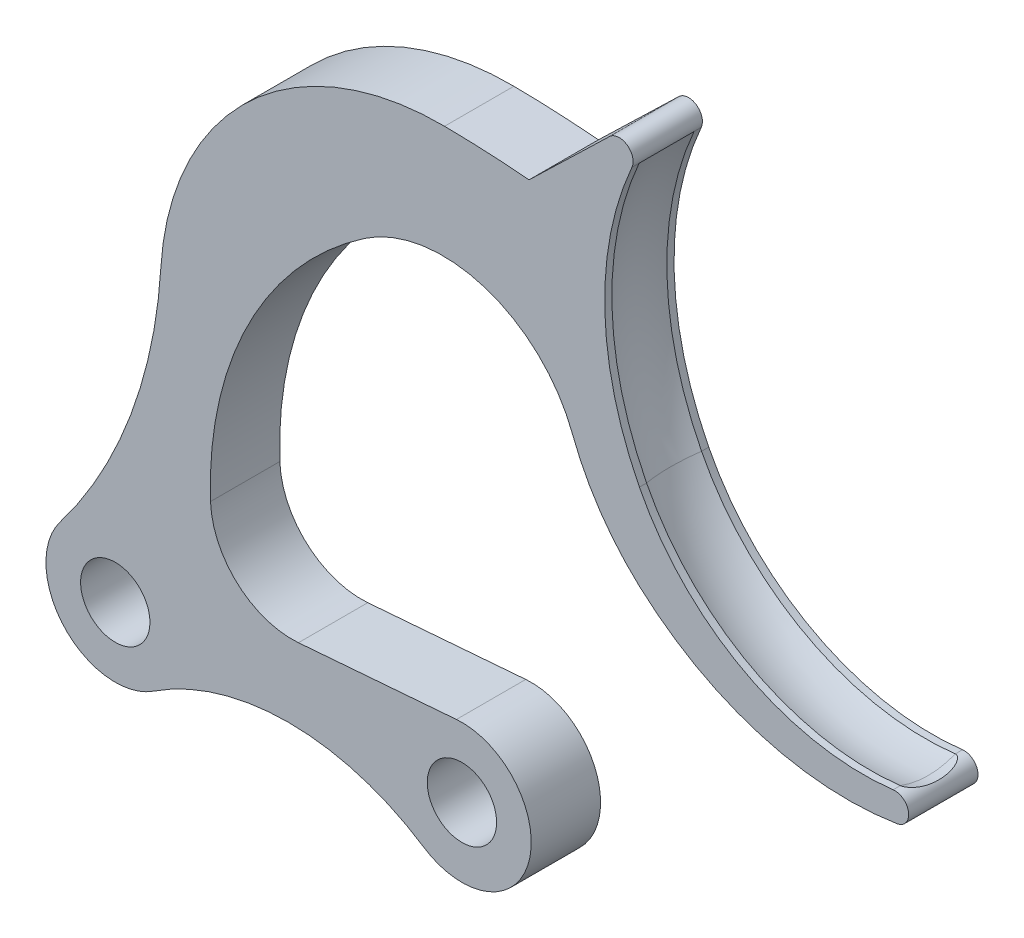
SolidWorks part; units mm, degrees
ref_plane "前基準面" through (0, 0, 0) normal (0, 0, 1) x (1, 0, 0)
ref_plane "上基準面" through (0, 0, 0) normal (0, 1, 0) x (1, 0, 0)
ref_plane "右基準面" through (0, 0, 0) normal (1, 0, 0) x (0, 0, -1)
sketch "草圖1" plane through (0, 0, 0) normal (0, 0, 1) x (1, 0, 0)
  line L0 (0, 0) -> (4.7, 36.1961) construction
  line L1 (4.7, 36.1961) -> (25, 0) construction
  line L2 (25, 0) -> (0, 0) construction
  line L3 (0, -5) -> (25, -5)
  line L4 (29.361, 2.4458) -> (15.0641, 27.938)
  line L5 (-1.4143, 27.938) -> (-4.9584, 0.6438)
  line L6 (15.0641, 27.938) -> (44.9947, 27.938)
  line L7 (-20.7636, 63.3928) -> (44.9947, 63.3928)
  line L8 (-20.7636, 63.3928) -> (-20.7636, 27.938)
  line L9 (-20.7636, 27.938) -> (-1.4143, 27.938)
  line L10 (44.9947, 63.3928) -> (44.9947, 27.938)
  circle A0 centre (25, 0) radius 2.5
  circle A2 centre (0, 0) radius 2.5
  arc A3 (-4.9584, 0.6438) -> (0, -5) centre (0, 0) ccw
  arc A4 (25, -5) -> (29.361, 2.4458) centre (25, 0) ccw
  circle A7 centre (25, 0) radius 5 construction
  circle A8 centre (0, 0) radius 5 construction
  dimension "D3" = 5
  dimension "D1" = 25
  dimension "D2" = 41.5
  dimension "36.5" = 36.5
  dimension "D4" = 2.5
extrude "填料-伸長1" add sketch "草圖1" along normal mid plane 5
sketch "草圖2" plane through (0, 0, 2.5) normal (0, 0, 1) x (1, 0, 0)
  line L0 (31.9587, 36.1505) -> (34.5621, 40.7499)
  line L1 (13.2102, 4.0796) -> (24.6043, 4.9843)
  arc A0 (25, -5) -> (29.361, 2.4458) centre (25, 0) ccw construction
  arc A1 (-4.9584, 0.6438) -> (0, -5) centre (0, 0) ccw construction
  arc A2 (6.8693, 9.7274) -> (31.9587, 36.1505) centre (32.354, 10.6522) cw
  arc A3 (22.2498, -4.1757) -> (24.6043, 4.9843) centre (25, 0) ccw
  arc A4 (-3.974, 3.0343) -> (2.7502, -4.1757) centre (0, 0) ccw
  arc A5 (3.2871, 22.5416) -> (23.7482, 41.6042) centre (23.5417, 21.3134) cw
  arc A6 (6.8693, 9.7274) -> (13.2102, 4.0796) centre (12.7448, 9.9406) ccw
  arc A7 (3.2871, 22.5416) -> (-3.974, 3.0343) centre (-32.3526, 24.7027) cw
  arc A8 (2.7502, -4.1757) -> (22.2498, -4.1757) centre (12.5, -18.9787) cw
  arc A9 (23.7482, 41.6042) -> (34.5621, 40.7499) centre (22.9439, -37.4448) cw
extrude "除料-伸長1" cut sketch "草圖2" against normal blind 5 flip side to cut
sketch "草圖6" plane through (0, 0, 2.5) normal (0, 0, 1) x (1, 0, 0)
  line L0 (29.8437, 41.3066) -> (35.6487, 46.9142)
  line L7 (31.9587, 36.1505) -> (34.5621, 40.7499)
  arc A0 (37.3982, 45.5681) -> (37.1726, 29.2406) centre (73.0041, 36.9109) ccw construction
  arc A1 (37.1726, 29.2406) -> (46.5702, 19.2347) centre (50.1577, 32.0203) ccw construction
  arc A2 (31.9587, 36.1505) -> (37.7992, 19.902) centre (50.2241, 33.5421) ccw
  arc A3 (37.7992, 19.902) -> (56.378, 14.3602) centre (52.8406, 36.4145) ccw
  arc A4 (56.0999, 16.3404) -> (56.378, 14.3602) centre (56.2196, 15.3476) cw
  arc A6 (34.5621, 40.7499) -> (23.7482, 41.6042) centre (22.9439, -37.4448) ccw construction
  arc A7 (35.6487, 46.9142) -> (37.2579, 45.7901) centre (36.3435, 46.1949) cw
  arc A8 (34.5621, 40.7499) -> (29.8437, 41.3066) centre (22.9439, -37.4448) ccw
  arc A9 (37.2579, 45.7901) -> (37.7992, 26.0908) centre (58.2227, 36.5091) ccw
  arc A10 (37.7992, 26.0908) -> (56.0999, 16.3404) centre (53.9314, 34.32) ccw
  point P15 (56.2196, 16.3404)
  point P25 (37.7992, 26.0908)
  point P26 (52.6368, 17.7185)
  point P27 (52.1842, 17.2802)
  dimension "D1" = 1
  dimension "D2" = 1
extrude "填料-伸長3" add sketch "草圖6" against normal blind 5
sketch "草圖16" plane through (0, 0, 0) normal (0, 0, 1) x (1, 0, 0)
  arc A4 (37.7992, 26.0908) -> (56.0999, 16.3404) centre (53.9314, 34.32) ccw construction
  arc A5 (37.2579, 45.7901) -> (37.7992, 26.0908) centre (58.2227, 36.5091) ccw construction
  arc A6 (37.7992, 26.0908) -> (56.0999, 16.3404) centre (53.9314, 34.32) ccw
  arc A7 (37.2579, 45.7901) -> (37.7992, 26.0908) centre (58.2227, 36.5091) ccw
ref_plane "平面2" through (37.2579, 45.7901, 2.5) normal (0.4048, 0.9144, 0) x (0.9144, -0.4048, 0)
sketch "草圖9" plane through (37.2579, 45.7901, 2.5) normal (0.4048, 0.9144, 0) x (0.9144, -0.4048, 0)
  line L0 (0, 2.5) -> (5.6632, 2.5) construction
  line L1 (0, 5) -> (0, 0) construction
  circle A0 centre (5.6632, 2.5) radius 6
  point P3 (5.2514, 2.5)
  point P7 (5.6632, 2.5)
  dimension "D1" = 12
sweep "除料-掃出3" cut profiles "草圖9" path "草圖16"
fillet "圓角1" radius 10 1 edges at (31.9587, 36.1505, 0)
sketch "草圖20" plane through (57.2381, 6.9033, 0) normal (-0.9928, -0.1197, 0) x (0, 0, 1)
  line L1 (1.982, 9.5055) -> (-1.982, 9.5055)
  line L2 (1.982, 9.5055) -> (-1.982, 9.5055)
  arc A2 (-1.982, 9.5055) -> (0, 9.1686) centre (0, 15.1686) ccw
  arc A3 (0, 9.1686) -> (1.982, 9.5055) centre (0, 15.1686) ccw
  arc A4 (-1.982, 9.5055) -> (0, 9.1686) centre (0, 15.1686) ccw
  arc A5 (0, 9.1686) -> (1.982, 9.5055) centre (0, 15.1686) ccw
  dimension "D1" = 0
extrude "除料-伸長2" cut sketch "草圖20" against normal blind 10
